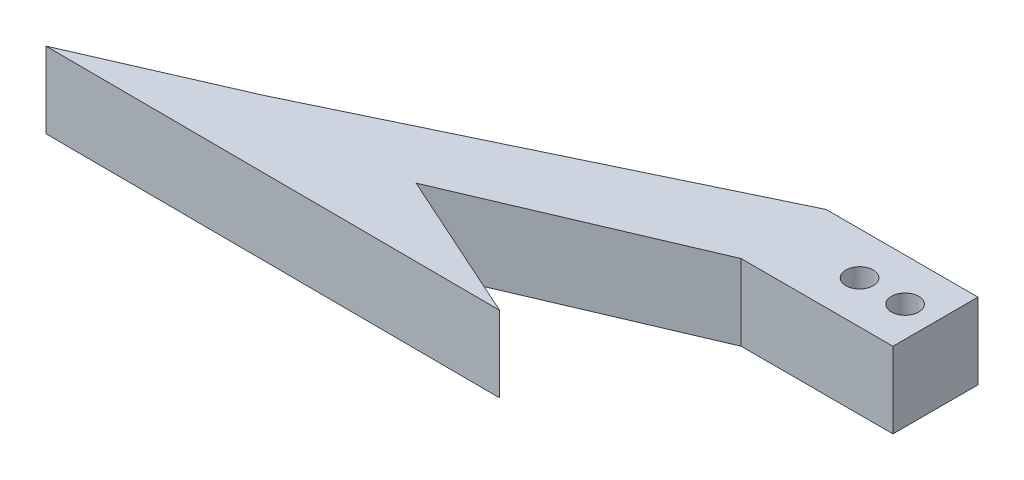
SolidWorks part; units mm, degrees
ref_plane "Front Plane" through (0, 0, 0) normal (0, 0, 1) x (1, 0, 0)
ref_plane "Top Plane" through (0, 0, 0) normal (0, 1, 0) x (1, 0, 0)
ref_plane "Right Plane" through (0, 0, 0) normal (1, 0, 0) x (0, 0, -1)
sketch "Sketch2" plane through (0, 0, 0) normal (0, 1, 0) x (1, 0, 0)
  line L4 (0, 3.556) -> (0, -3.556)
  line L5 (0, -3.556) -> (-12.7, -3.556)
  line L6 (-12.7, -3.556) -> (-12.7, 3.556)
  line L7 (-12.7, 3.556) -> (0, 3.556)
  line L8 (-44.45, -11.684) -> (-31.75, -11.684)
  line L11 (-31.75, -11.684) -> (-25.4, -18.034)
  line L12 (-25.4, -18.034) -> (-50.8, -18.034)
  line L13 (-50.8, -18.034) -> (-44.45, -11.684)
  line L14 (-12.7, 3.556) -> (-44.45, -11.684)
  line L15 (-12.7, -3.556) -> (-31.75, -11.684)
  line L16 (-44.45, -11.684) -> (-31.75, -11.684)
  line L17 (-12.7, 3.556) -> (-12.7, -3.556)
  circle A0 centre (-2.54, 0) radius 1.143
  circle A1 centre (-6.35, 0) radius 1.143
  point P10 (-12.7, 0)
  dimension "D3" = 2.286
  dimension "D4" = 2.286
  dimension "D1" = 7.112
  dimension "D2" = 6.35
  dimension "D5" = 3.81
  dimension "D6" = 2.54
  dimension "D7" = 25.4
  dimension "D8" = 12.7
  dimension "D9" = 6.35
  dimension "D10" = 6.35
  dimension "D11" = 50.8
  dimension "D12" = 18.034
extrude "Boss-Extrude1" add sketch "Sketch2" along normal blind 6.35 contours L15 L6 L14 L8 | L7 L6 L5 L4 A1 A0
sketch "Sketch3" plane through (0, 0, 0) normal (0, 1, 0) x (1, 0, 0)
  line L0 (-44.45, -11.684) -> (-57.15, -17.2316)
  line L1 (-57.15, -17.2316) -> (-19.05, -17.3978)
  line L2 (-19.05, -17.3978) -> (-31.75, -11.684)
  line L3 (-44.45, -11.684) -> (-31.75, -11.684) construction
  line L10 (-31.75, -11.684) -> (-12.7, -3.556)
  line L11 (-12.7, -3.556) -> (0, -3.556)
  line L12 (0, -3.556) -> (0, 3.556)
  line L13 (0, 3.556) -> (-12.7, 3.556)
  line L14 (-12.7, 3.556) -> (-44.45, -11.684)
  line L15 (-44.45, -11.684) -> (-31.75, -11.684)
  line L21 (-44.45, -11.684) -> (-31.75, -11.684)
  dimension "D1" = 38.1
  dimension "D2" = 12.7
  dimension "D3" = 0.25
  dimension "D5" = 0
extrude "Boss-Extrude2" add sketch "Sketch3" along normal blind 6.35
